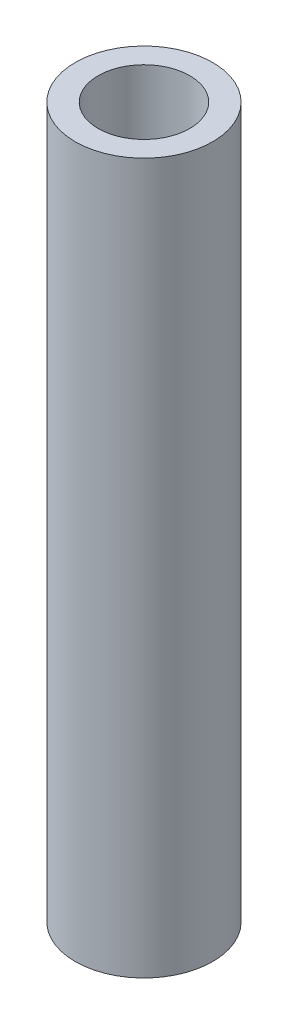
SolidWorks part; units mm, degrees
ref_plane "Front Plane" through (0, 0, 0) normal (0, 0, 1) x (1, 0, 0)
ref_plane "Top Plane" through (0, 0, 0) normal (0, 1, 0) x (1, 0, 0)
ref_plane "Right Plane" through (0, 0, 0) normal (1, 0, 0) x (0, 0, -1)
sketch "Sketch1" plane through (0, 0, 0) normal (0, 1, 0) x (1, 0, 0)
  circle A0 centre (0, 0) radius 4
  circle A1 centre (0, 0) radius 6
  dimension "D1" = 8
  dimension "D2" = 2
extrude "Boss-Extrude1" add sketch "Sketch1" along normal blind 62
